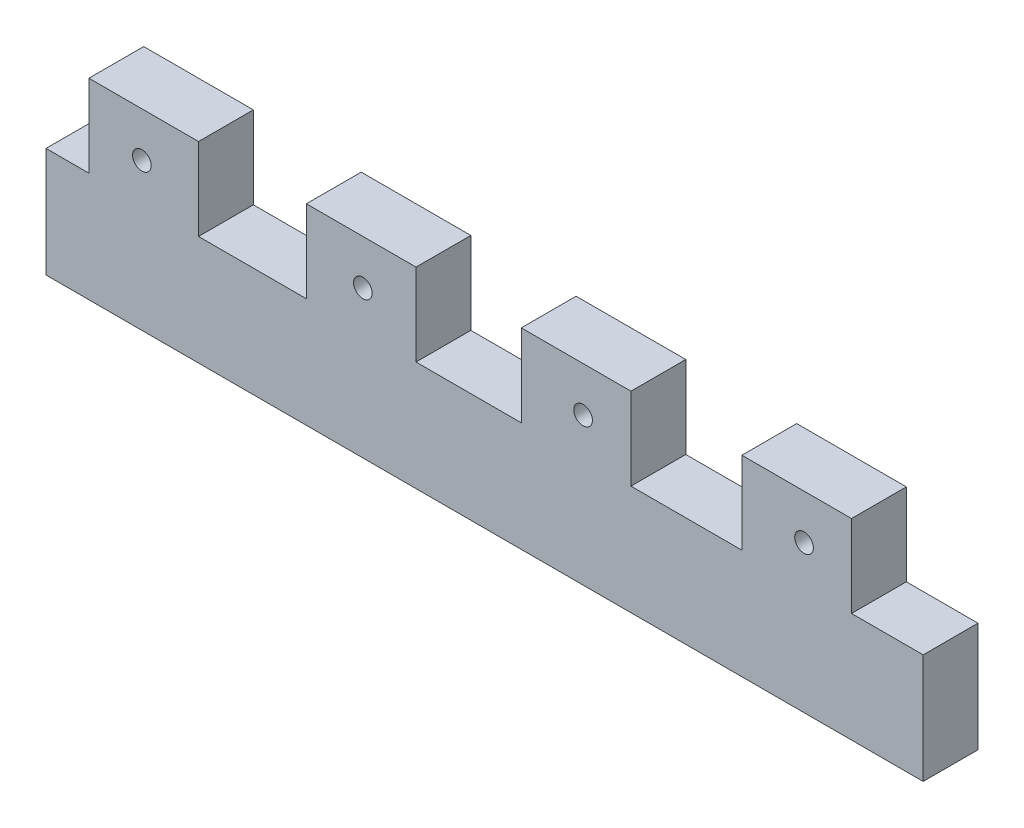
SolidWorks part; units mm, degrees
ref_plane "Front Plane" through (0, 0, 0) normal (0, 0, 1) x (1, 0, 0)
ref_plane "Top Plane" through (0, 0, 0) normal (0, 1, 0) x (1, 0, 0)
ref_plane "Right Plane" through (0, 0, 0) normal (1, 0, 0) x (0, 0, -1)
sketch "Sketch2" plane through (0, 0, 0) normal (0, 0, 1) x (1, 0, 0)
  line L1 (0, 0) -> (101.6, 0)
  line L2 (0, 0) -> (0, 12.7)
  line L3 (0, 12.7) -> (101.6, 12.7)
  line L4 (101.6, 0) -> (101.6, 12.7)
  line L5 (4.9664, 12.7) -> (17.6664, 12.7)
  line L6 (4.9664, 12.7) -> (4.9664, 22.225)
  line L7 (4.9664, 22.225) -> (17.6664, 22.225)
  line L8 (17.6664, 12.7) -> (17.6664, 22.225)
  line L9 (30.1579, 12.7) -> (42.8579, 12.7)
  line L10 (30.1579, 12.7) -> (30.1579, 22.225)
  line L11 (30.1579, 22.225) -> (42.8579, 22.225)
  line L12 (42.8579, 12.7) -> (42.8579, 22.225)
  line L13 (55.0512, 12.7) -> (67.7512, 12.7)
  line L14 (55.0512, 12.7) -> (55.0512, 22.225)
  line L15 (55.0512, 22.225) -> (67.7512, 22.225)
  line L16 (67.7512, 12.7) -> (67.7512, 22.225)
  line L17 (80.6005, 12.7) -> (93.3005, 12.7)
  line L18 (80.6005, 12.7) -> (80.6005, 22.225)
  line L19 (80.6005, 22.225) -> (93.3005, 22.225)
  line L20 (93.3005, 12.7) -> (93.3005, 22.225)
  dimension "D1" = 12.7
  dimension "D2" = 101.6
  dimension "D3" = 12.7
  dimension "D4" = 9.525
extrude "Boss-Extrude1" add sketch "Sketch2" along normal blind 6.35 contours L3 L8 L7 L6 | L1 L4 L3 L2 | L3 L12 L11 L10 | L3 L16 L15 L14 | L3 L20 L19 L18
sketch "Sketch1" plane through (0, 0, 0) normal (0, 0, 1) x (1, 0, 0)
  circle A0 centre (87.7987, 17.0582) radius 1.0795
  circle A4 centre (62.2062, 17.0582) radius 1.0795
  circle A5 centre (36.6987, 17.0582) radius 1.0795
  circle A6 centre (11.1062, 17.0582) radius 1.0795
  circle A7 centre (31.3261, 115.3905) radius 1.0795
  circle A8 centre (56.9186, 115.3905) radius 1.0795
  circle A9 centre (82.4261, 115.3905) radius 1.0795
  circle A10 centre (108.0186, 115.3905) radius 1.0795
  point P2 (3.3906, 17.0196)
  point P3 (62.2062, 17.0582)
  dimension "D1" = 2.159
  dimension "D5" = 25.5925
  dimension "D6" = 25.5075
  dimension "D4" = 25.5925
extrude "Cut-Extrude2" cut sketch "Sketch1" along normal through all
